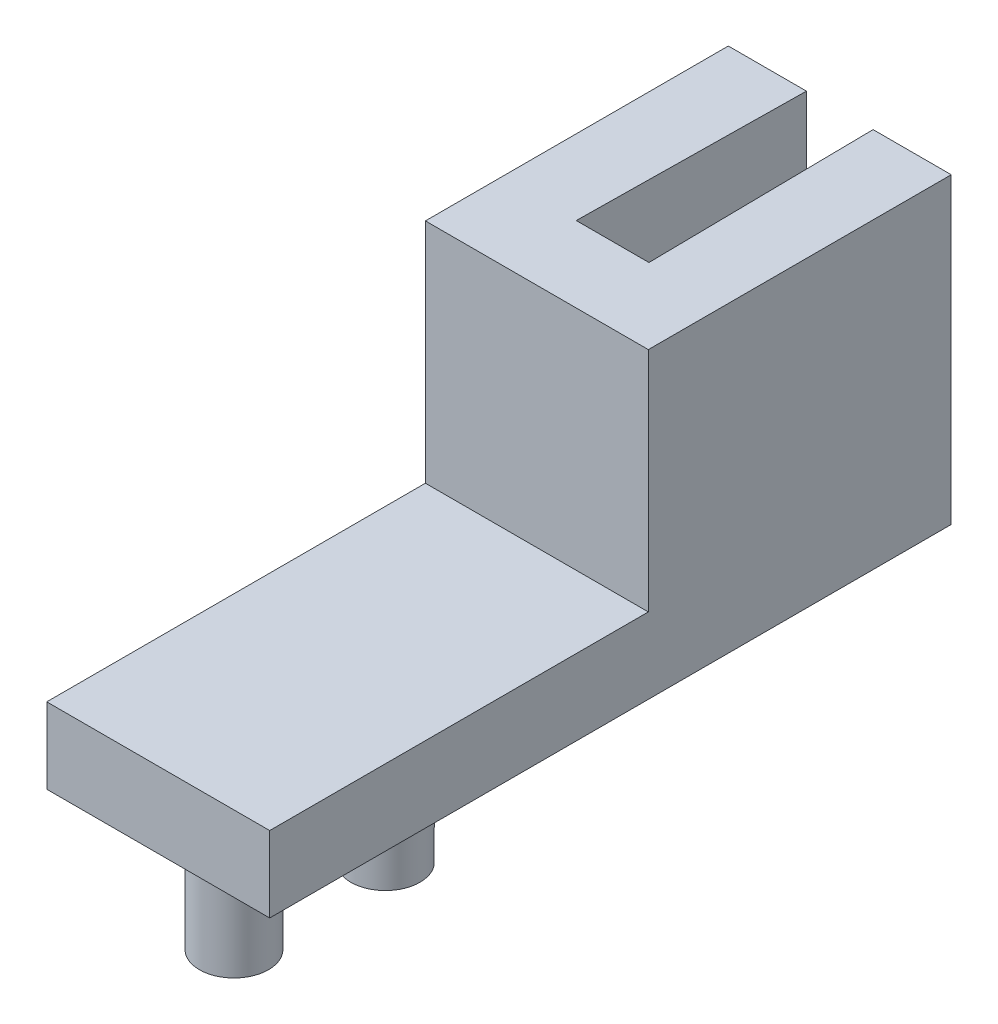
SolidWorks part; units mm, degrees
ref_plane "Front Plane" through (0, 0, 0) normal (0, 0, 1) x (1, 0, 0)
ref_plane "Top Plane" through (0, 0, 0) normal (0, 1, 0) x (1, 0, 0)
ref_plane "Right Plane" through (0, 0, 0) normal (1, 0, 0) x (0, 0, -1)
sketch "Sketch2" plane through (0, 0, 0) normal (1, 0, 0) x (0, 0, -1)
  line L0 (3.175, 9.525) -> (3.175, -3.175) construction
  line L1 (-15.875, 0) -> (0, 0)
  line L2 (-15.875, 0) -> (-15.875, -3.175)
  line L3 (-15.875, -3.175) -> (0, -3.175)
  line L4 (0, 0) -> (0, -3.175)
  line L5 (0, -3.175) -> (12.7, -3.175)
  line L6 (0, -3.175) -> (0, 9.525)
  line L7 (0, 9.525) -> (12.7, 9.525)
  line L8 (12.7, -3.175) -> (12.7, 9.525)
  line L9 (-6.35, 0) -> (-6.35, -3.175) construction
  line L10 (-12.7, 0) -> (-12.7, -3.175) construction
  dimension "D1" = 12.7
  dimension "D2" = 3.175
  dimension "D3" = 3.175
  dimension "D4" = 9.525
  dimension "D5" = 6.35
  dimension "D6" = 12.7
  dimension "D7" = 3.175
extrude "Boss-Extrude1" add sketch "Sketch2" along normal blind 9.3472 contours L4 L1 L2 L3 | L5 L8 L7 L6 L4
sketch "Sketch3" plane through (0, 9.525, 0) normal (0, 1, 0) x (1, 0, 0)
  line L0 (9.3472, 12.7) -> (0, 12.7) construction
  line L1 (3.2766, 12.7) -> (6.0706, 12.7)
  line L2 (3.2766, 12.7) -> (3.1496, 3.175)
  line L3 (3.1496, 3.175) -> (6.1976, 3.175)
  line L4 (6.0706, 12.7) -> (6.1976, 3.175)
  line L5 (9.3472, 0) -> (0, 0) construction
  line L6 (9.3472, 0) -> (0, 0) construction
  line L7 (3.1496, 3.175) -> (3.1496, 12.7)
  line L8 (6.1976, 3.175) -> (6.1976, 12.7)
  line L9 (6.1976, 12.7) -> (3.1496, 12.7)
  point P6 (4.6736, 3.175)
  point P9 (4.6736, 0)
  point P12 (5.4138, 12.7)
  point P13 (3.8873, 12.7)
  point P14 (12.2084, 12.7)
  point P17 (4.6736, 12.7)
  point P18 (4.6736, 12.7)
  dimension "D3" = 2.794
  dimension "D1" = 3.048
  dimension "D2" = 3.175
extrude "Cut-Extrude1" cut sketch "Sketch3" against normal through all
sketch "Sketch4" plane through (0, -3.175, 0) normal (0, -1, 0) x (1, 0, 0)
  line L0 (3.1496, -3.175) -> (6.1976, -3.175) construction
  circle A0 centre (4.6736, 12.7) radius 1.45
  circle A2 centre (4.6736, 6.35) radius 1.45
  point P7 (4.6736, -3.175)
  dimension "D1" = 2.9
extrude "Boss-Extrude2" add sketch "Sketch4" along normal blind 5.08
